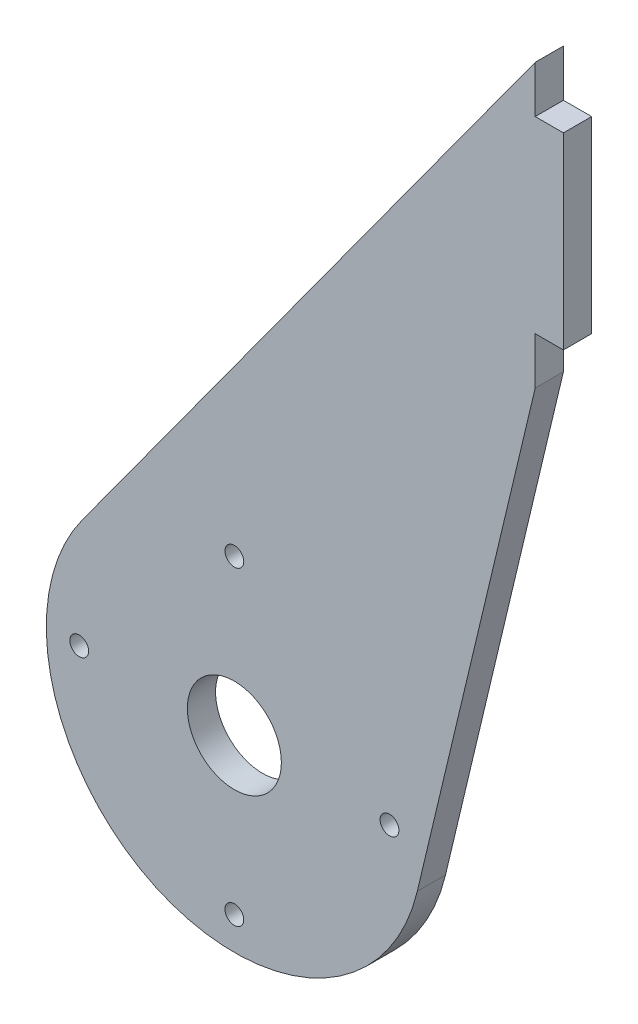
SolidWorks part; units mm, degrees
ref_plane "Front Plane" through (0, 0, 0) normal (0, 0, 1) x (1, 0, 0)
ref_plane "Top Plane" through (0, 0, 0) normal (0, 1, 0) x (1, 0, 0)
ref_plane "Right Plane" through (0, 0, 0) normal (1, 0, 0) x (0, 0, -1)
sketch "Sketch1" plane through (0, 0, 0) normal (0, 0, 1) x (1, 0, 0)
  line L0 (-16.1744, 11.7639) -> (32, 78)
  line L1 (32, 78) -> (32, 48)
  line L2 (32, 48) -> (19.4551, -4.6367)
  arc A0 (-16.1744, 11.7639) -> (19.4551, -4.6367) centre (0, 0) ccw
  circle A5 centre (0, 16.5) radius 1
  circle A6 centre (-16.5, 0) radius 1
  circle A7 centre (0, -16.5) radius 1
  circle A8 centre (16.5, 0) radius 1
  dimension "D1" = 2
  dimension "D2" = 20
  dimension "D3" = 16.5
  dimension "D4" = 19.4551
  dimension "D5" = 32
  dimension "D6" = 16.1744
  dimension "D7" = 16.5
  dimension "D8" = 16.5
  dimension "D9" = 16.5
extrude "Boss-Extrude1" add sketch "Sketch1" against normal blind 3
sketch "Sketch2" plane through (0, 0, 0) normal (0, 0, 1) x (1, 0, 0)
  circle A0 centre (0, 0) radius 5
  dimension "D1" = 10
extrude "Cut-Extrude1" cut sketch "Sketch2" against normal blind 10
sketch "Sketch4" plane through (32, 0, 0) normal (1, 0, 0) x (0, 0, -1)
  line L0 (0, 48) -> (0, 78) construction
  line L1 (0, 73) -> (3, 73)
  line L2 (0, 73) -> (0, 53)
  line L3 (0, 53) -> (3, 53)
  line L4 (3, 73) -> (3, 53)
  line L5 (3, 48) -> (3, 78) construction
  line L6 (3, 48) -> (0, 48) construction
  dimension "D1" = 20
  dimension "D2" = 5
extrude "Boss-Extrude3" add sketch "Sketch4" along normal blind 3
